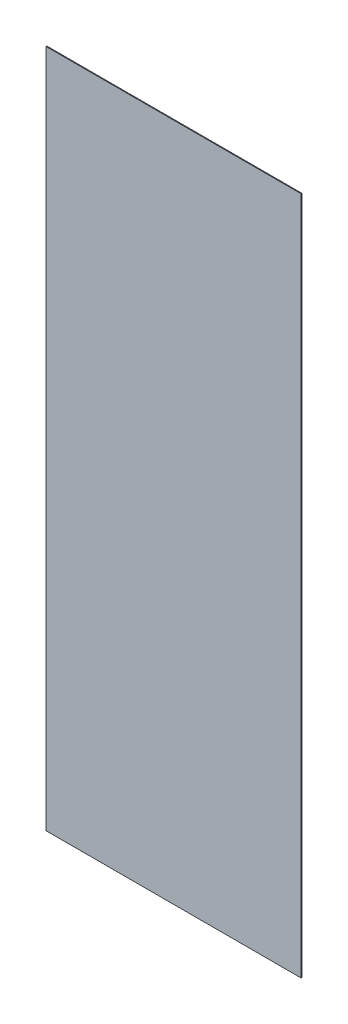
SolidWorks part; units mm, degrees
ref_plane "정면" through (0, 0, 0) normal (0, 0, 1) x (1, 0, 0)
ref_plane "윗면" through (0, 0, 0) normal (0, 1, 0) x (1, 0, 0)
ref_plane "우측면" through (0, 0, 0) normal (1, 0, 0) x (0, 0, -1)
sketch "스케치1" plane through (0, 0, 0) normal (0, 0, 1) x (1, 0, 0)
  line L1 (0, 0) -> (308, 0)
  line L2 (0, 0) -> (0, 820)
  line L3 (0, 820) -> (308, 820)
  line L4 (308, 0) -> (308, 820)
  dimension "D1" = 820
  dimension "D2" = 308
extrude "보스-돌출1" add sketch "스케치1" along normal blind 1
